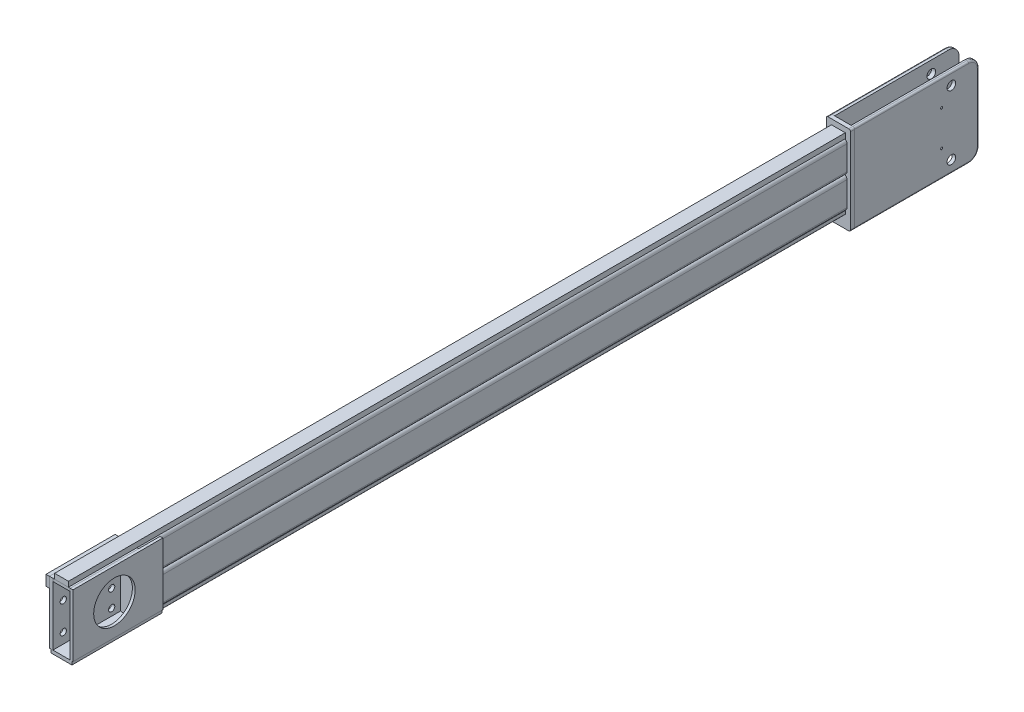
SolidWorks part; units mm, degrees
other "焊接文件夹"
material "普通碳钢"
ref_plane "前视基准面" through (0, 0, 0) normal (0, 0, 1) x (1, 0, 0)
ref_plane "上视基准面" through (0, 0, 0) normal (0, 1, 0) x (1, 0, 0)
ref_plane "右视基准面" through (0, 0, 0) normal (1, 0, 0) x (0, 0, -1)
sketch "草图1" plane through (0, 0, 0) normal (1, 0, 0) x (0, 0, -1)
  line L0 (0, 0) -> (2050, 0)
  dimension "D1" = 2050
other "矩形钢管 90×60×5(1)"
ref_plane "基准面1" through (15, 55, 0) normal (0, 0, -1) x (1, 0, 0)
sketch "草图11" plane through (15, 55, 0) normal (0, 0, -1) x (1, 0, 0)
  line L0 (-15, 50) -> (15, 50)
  line L1 (-15, -35) -> (15, -35)
  line L2 (-25, -25) -> (-25, 45)
  line L3 (-15, 55) -> (15, 55)
  line L4 (25, -25) -> (25, 45)
  line L7 (20, -25) -> (20, 45)
  line L8 (-15, -30) -> (15, -30)
  line L9 (-20, -25) -> (-20, 45)
  arc A0 (15, 55) -> (25, 45) centre (15, 45) cw
  arc A1 (15, -35) -> (25, -25) centre (15, -25) ccw
  arc A2 (-15, -35) -> (-25, -25) centre (-15, -25) cw
  arc A3 (-25, 45) -> (-15, 55) centre (-15, 45) cw
  arc A4 (-20, 45) -> (-15, 50) centre (-15, 45) cw
  arc A5 (15, 50) -> (20, 45) centre (15, 45) cw
  arc A6 (15, -30) -> (20, -25) centre (15, -25) ccw
  arc A7 (-15, -30) -> (-20, -25) centre (-15, -25) cw
  point P0 (0, 0)
  point P1 (0, 0)
  point P30 (0, 0)
  point P32 (-25, 35)
  point P33 (-25, -35)
  point P34 (25, -35)
  point P35 (25, 35)
  dimension "D3" = 10
  dimension "D1" = 50
  dimension "D2" = 90
  dimension "D4" = 5
other "矩形钢管 90×60×5(3)"
ref_plane "基准面2" through (15, -35, 0) normal (0, 0, -1) x (1, 0, 0)
sketch "草图12" plane through (15, -35, 0) normal (0, 0, -1) x (1, 0, 0)
  line L0 (-15, 50) -> (15, 50)
  line L1 (-15, -35) -> (15, -35)
  line L2 (-25, -25) -> (-25, 45)
  line L3 (-15, 55) -> (15, 55)
  line L4 (25, -25) -> (25, 45)
  line L7 (20, -25) -> (20, 45)
  line L8 (-15, -30) -> (15, -30)
  line L9 (-20, -25) -> (-20, 45)
  arc A0 (15, 55) -> (25, 45) centre (15, 45) cw
  arc A1 (15, -35) -> (25, -25) centre (15, -25) ccw
  arc A2 (-15, -35) -> (-25, -25) centre (-15, -25) cw
  arc A3 (-25, 45) -> (-15, 55) centre (-15, 45) cw
  arc A4 (-20, 45) -> (-15, 50) centre (-15, 45) cw
  arc A5 (15, 50) -> (20, 45) centre (15, 45) cw
  arc A6 (15, -30) -> (20, -25) centre (15, -25) ccw
  arc A7 (-15, -30) -> (-20, -25) centre (-15, -25) cw
  point P0 (0, 0)
  point P1 (0, 0)
  point P30 (0, 0)
  point P32 (-25, 35)
  point P33 (-25, -35)
  point P34 (25, -35)
  point P35 (25, 35)
  dimension "D3" = 10
  dimension "D1" = 50
  dimension "D2" = 90
  dimension "D4" = 5
ref_plane "基准面3" through (30, 0, 0) normal (1, 0, 0) x (0, 0, -1)
sketch "草图13" plane through (30, 0, 0) normal (1, 0, 0) x (0, 0, -1)
  line L0 (0, 0) -> (2050, 0)
sketch "草图14" plane through (0, 0, 0) normal (0, 0, 1) x (1, 0, 0)
  line L2 (45, 80) -> (45, -80)
  line L3 (0, -85) -> (40, -85)
  line L4 (-5, 80) -> (-5, -80)
  line L5 (0, 85) -> (40, 85)
  arc A0 (40, -85) -> (45, -80) centre (40, -80) ccw
  arc A1 (-5, -80) -> (0, -85) centre (0, -80) ccw
  arc A4 (0, 85) -> (-5, 80) centre (0, 80) ccw
  arc A5 (45, 80) -> (40, 85) centre (40, 80) ccw
extrude "凸台-拉伸1" add sketch "草图14" along normal blind 8 separate body
sketch "草图15" plane through (0, 0, -2050) normal (0, 0, -1) x (-1, 0, 0)
  line L0 (-50, 115) -> (-50, -131)
  line L1 (-45, 120) -> (15, 120)
  line L3 (-45, -136) -> (15, -136)
  line L5 (-40, 80) -> (-40, 10) construction
  line L6 (20, -131) -> (20, 115)
  line L7 (10, 10) -> (10, 80) construction
  line L8 (0, 90) -> (-30, 90) construction
  line L9 (-30, -90) -> (0, -90) construction
  arc A0 (15, -136) -> (20, -131) centre (15, -131) ccw
  arc A1 (-50, -131) -> (-45, -136) centre (-45, -131) ccw
  arc A2 (20, 115) -> (15, 120) centre (15, 115) ccw
  arc A3 (-50, 115) -> (-45, 120) centre (-45, 115) cw
  dimension "D5" = 5
  dimension "D1" = 30
  dimension "D2" = 10
  dimension "D3" = 10
  dimension "D4" = 46
extrude "凸台-拉伸2" add sketch "草图15" along normal blind 12 separate body
sketch "草图16" plane through (0, 0, -2062) normal (0, 0, -1) x (-1, 0, 0)
  line L0 (-45, -136) -> (15, -136) construction
  line L1 (-40, -136) -> (-50, -136)
  line L2 (-40, -136) -> (-40, 120)
  line L3 (-40, 120) -> (-50, 120)
  line L4 (-50, -136) -> (-50, 120)
  line L6 (15, 120) -> (-45, 120) construction
  line L11 (8, 120) -> (20, 120)
  line L12 (8, 120) -> (8, -136)
  line L13 (8, -136) -> (20, -136)
  line L14 (20, 120) -> (20, -136)
  line L15 (20, -131) -> (20, 115) construction
  line L16 (-50, 115) -> (-50, -131) construction
  dimension "D1" = 12
  dimension "D2" = 10
extrude "凸台-拉伸3" add sketch "草图16" along normal blind 360 separate body
fillet "圆角4" radius 30 2 edges at (45, -136, -2422) (45, 120, -2422)
fillet "圆角5" radius 30 2 edges at (-14, -136, -2422) (-14, 120, -2422)
fillet "圆角1" radius 5 5 edges at (50, -136, -2227) (50, 120, -2227) (50, -127.2132, -2413.2132) (50, -8, -2422) (50, 111.2132, -2413.2132)
fillet "圆角2" radius 5 5 edges at (-20, -136, -2227) (-20, 120, -2227) (-20, -127.2132, -2413.2132) (-20, -8, -2422) (-20, 111.2132, -2413.2132)
sketch "草图17" plane through (0, -90, 0) normal (0, -1, 0) x (1, 0, 0)
  line L0 (-10, -2050) -> (-10, 0) construction
  line L1 (35, -60) -> (-5, -60)
  line L2 (35, -60) -> (35, -2050)
  line L3 (35, -2050) -> (-5, -2050)
  line L4 (-5, -60) -> (-5, -2050)
  line L5 (30, -2050) -> (0, -2050) construction
  line L6 (30, 0) -> (0, 0) construction
  dimension "D1" = 40
  dimension "D2" = 5
  dimension "D3" = 60
extrude "凸台-拉伸4" add sketch "草图17" along normal blind 10 separate body
fillet "圆角6" radius 1 2 edges at (35, -100, -1055) (-5, -100, -1055)
sketch "草图18" plane through (-20, 0, 0) normal (-1, 0, 0) x (0, 0, 1)
  line L0 (-2342, 85) -> (-2342, -101) construction
  line L1 (-2392, 120) -> (-2062, 120) construction
  line L2 (-2062, -136) -> (-2392, -136) construction
  line L3 (-2062, -131) -> (-2062, 115) construction
  circle A0 centre (-2342, 85) radius 12.5
  circle A1 centre (-2342, -101) radius 12.5
  dimension "D1" = 25
  dimension "D2" = 25
  dimension "D3" = 35
  dimension "D4" = 35
  dimension "D5" = 280
extrude "切除-拉伸1" cut sketch "草图18" against normal up to surface (70 mm away)
sketch "草图19" plane through (50, 0, 0) normal (1, 0, 0) x (0, 0, -1)
  point P0 (2314, 42.75)
  point P1 (2314, -58.75)
hole_wizard "M6 螺纹孔1" positions "3D草图1" profile "草图20" tap size "M6" standard "GB" end condition up to next
sketch3d "3D草图1"
  point P0 (50, 42.75, -2314)
  point P3 (50, -58.75, -2314)
sketch "草图20" plane through (50, 42.75, -2314) normal (0, 1, 0) x (0, 0, -1)
  line L0 (0, 0) -> (0, 10.001)
  line L1 (0, 10.001) -> (2.5, 10.001)
  line L2 (2.5, 10.001) -> (2.5, 0.525)
  line L3 (2.5, 0.525) -> (3.025, 0)
  line L5 (3.025, 0) -> (0, 0)
  line L6 (-2.5, 0.525) -> (-3.025, 0) construction
  line L11 (0, -6.35) -> (0, 107.95) construction
  dimension "螺纹线主直径" = 5
  dimension "通孔螺纹孔钻头深度" = 10.001
  dimension "近端锥形沉头孔直径" = 6.05
  dimension "近端锥形沉头孔角度" = 90
sketch "草图21" plane through (0, 0, 8) normal (0, 0, 1) x (1, 0, 0)
  line L1 (-15, -100) -> (45, -100)
  line L2 (-15, -100) -> (-15, -90)
  line L3 (-15, -90) -> (45, -90)
  line L4 (45, -100) -> (45, -90)
  line L6 (35, -90) -> (-5, -90) construction
  line L7 (-10, -80) -> (-10, -10) construction
  line L8 (40, -10) -> (40, -80) construction
  dimension "D1" = 10
  dimension "D2" = 5
  dimension "D3" = 5
extrude "凸台-拉伸5" add sketch "草图21" along normal blind 190 separate body
ref_plane "基准面4" through (0, 0, -2) normal (0, 0, 1) x (1, 0, 0)
sketch "草图22" plane through (-10, 0, 0) normal (-1, 0, 0) x (0, 0, 1)
  line L0 (-2050, 90) -> (0, 90) construction
  line L1 (198, -90) -> (-62, -90)
  line L2 (198, -90) -> (198, 90)
  line L3 (198, 90) -> (-62, 90)
  line L4 (-62, -90) -> (-62, 90)
  dimension "D1" = 260
extrude "凸台-拉伸6" add sketch "草图22" along normal blind 10 separate body
sketch "草图23" plane through (40, 0, 0) normal (1, 0, 0) x (0, 0, -1)
  line L4 (-198, 90) -> (-198, -90)
  line L5 (-198, -90) -> (62, -90)
  line L6 (62, -90) -> (62, 90)
  line L7 (62, 90) -> (-198, 90)
  line L8 (-198, 90) -> (-198, -90)
  line L9 (-198, -90) -> (62, -90)
  line L10 (62, -90) -> (62, 90)
  line L11 (62, 90) -> (-198, 90)
  dimension "D1" = 0
extrude "凸台-拉伸7" add sketch "草图23" along normal blind 8 separate body
sketch "草图24" plane through (0, 90, 0) normal (0, 1, 0) x (1, 0, 0)
  line L1 (-10, 0) -> (40, 0)
  line L2 (-10, 0) -> (-10, -198)
  line L3 (-10, -198) -> (40, -198)
  line L4 (40, 0) -> (40, -198)
  line L6 (-10, -198) -> (-10, 62) construction
extrude "凸台-拉伸9" add sketch "草图24" against normal blind 8 separate body
sketch "草图25" plane through (48, 0, 0) normal (1, 0, 0) x (0, 0, -1)
  line L0 (-198, 90) -> (-198, -90) construction
  line L1 (-198, 0) -> (-78, 0) construction
  circle A0 centre (-78, 0) radius 60
  dimension "D1" = 120
  dimension "D2" = 120
extrude "切除-拉伸2" cut sketch "草图25" against normal up to next (8 mm away)
sketch "草图26" plane through (-20, 0, 0) normal (-1, 0, 0) x (0, 0, 1)
  line L0 (198, -60) -> (-62, -60) construction
  line L1 (28, -90) -> (28, 86.6904) construction
  line L2 (198, -90) -> (198, 90) construction
  line L4 (98, 97.709) -> (98, -90) construction
  line L5 (198, 30) -> (-62, 30) construction
  line L6 (198, -70) -> (-62, -70) construction
  line L7 (198, 20) -> (-62, 20) construction
  line L8 (198, 90) -> (-62, 90) construction
  line L9 (168, 125.1373) -> (168, -90) construction
  line L13 (-62, -90) -> (198, -90) construction
  line L14 (198, -20) -> (-62, -20) construction
  circle A6 centre (98, -20) radius 9
  circle A9 centre (98, 30) radius 9
  circle A11 centre (98, -70) radius 9
  circle A13 centre (168, -60) radius 9
  circle A14 centre (168, 20) radius 9
  circle A15 centre (28, -70) radius 9
  circle A16 centre (28, -20) radius 9
  circle A17 centre (28, 30) radius 9
  dimension "D3" = 30
  dimension "D6" = 70
  dimension "D2" = 50
  dimension "D7" = 18
  dimension "D9" = 18
  dimension "D10" = 18
  dimension "D11" = 18
  dimension "D12" = 18
  dimension "D15" = 18
  dimension "D16" = 18
  dimension "D17" = 18
  dimension "D13" = 70
  dimension "D14" = 110
  dimension "D4" = 40
  dimension "D5" = 40
  dimension "D8" = 50
extrude "切除-拉伸3" cut sketch "草图26" against normal up to next (10 mm away)
sketch "草图27" plane through (-20, 0, 0) normal (-1, 0, 0) x (0, 0, 1)
  line L6 (-2, 60) -> (198, 60)
  line L8 (198, 90) -> (198, 60)
  line L10 (-2, 90) -> (198, 90)
  line L11 (-2, 90) -> (-2, 60)
  line L14 (-2, 90) -> (-2, 245) construction
  line L15 (198, 90) -> (198, 245) construction
  line L16 (198, 90) -> (-62, 90) construction
  line L17 (198, -90) -> (198, 90) construction
  dimension "D1" = 30
  dimension "D2" = 200
extrude "凸台-拉伸10" add sketch "草图27" along normal blind 10 separate body
sketch "草图34" plane through (0, 0, 8) normal (0, 0, -1) x (-1, 0, 0)
  line L4 (15, -100) -> (15, -90)
  line L5 (15, -90) -> (-45, -90)
  line L6 (-45, -90) -> (-45, -100)
  line L7 (-45, -100) -> (15, -100)
  line L8 (15, -100) -> (15, -90)
  line L9 (15, -90) -> (-45, -90)
  line L10 (-45, -90) -> (-45, -100)
  line L11 (-45, -100) -> (15, -100)
  dimension "D1" = 0
extrude "凸台-拉伸15" add sketch "草图34" along normal up to surface (70 mm away) up to face at (-15, 0, -62)
sketch "草图28" plane through (0, 0, -2) normal (0, 0, 1) x (1, 0, 0)
  line L8 (-4, -100) -> (34, -100)
  line L9 (35, -99) -> (35, -90)
  line L10 (35, -90) -> (-5, -90)
  line L11 (-5, -90) -> (-5, -99)
  arc A4 (34, -100) -> (35, -99) centre (34, -99) ccw
  arc A5 (-5, -99) -> (-4, -100) centre (-4, -99) ccw
sketch "草图29" plane through (-20, 0, 0) normal (-1, 0, 0) x (0, 0, 1)
  line L0 (-2272, 30) -> (-2272, -70) construction
  line L1 (-2187, -70) -> (-2187, 30) construction
  line L2 (98, 30) -> (-3978.1522, 30) construction
  line L3 (-2422, -106) -> (-2422, 90) construction
  line L4 (-2102, 30) -> (-2102, -70) construction
  line L5 (-2272, -20) -> (-2102, -20) construction
  line L6 (-2272, -70) -> (-2102, -70) construction
  line L7 (-2272, -50) -> (-2102, -50) construction
  line L8 (-2272, 20) -> (-2102, 20) construction
  line L9 (-2167, -70) -> (-2167, 30) construction
  circle A3 centre (-2102, 30) radius 9
  circle A4 centre (-2102, -20) radius 9
  circle A5 centre (-2102, -70) radius 9
  circle A7 centre (-2187, -20) radius 9
  circle A8 centre (-2187, 30) radius 9
  circle A9 centre (-2272, 20) radius 9
  circle A10 centre (-2272, -50) radius 9
  circle A12 centre (-2187, -70) radius 9
  dimension "D2" = 18
  dimension "D3" = 18
  dimension "D8" = 18
  dimension "D9" = 18
  dimension "D10" = 18
  dimension "D11" = 20
  dimension "D12" = 18
  dimension "D13" = 18
  dimension "D4" = 50
  dimension "D5" = 50
  dimension "D6" = 150
  dimension "D7" = 170
  dimension "D14" = 30
  dimension "D16" = 85
  dimension "D15" = 40
extrude "切除-拉伸4" cut sketch "草图29" against normal up to next (12 mm away)
sketch "草图30" plane through (-20, 0, 0) normal (-1, 0, 0) x (0, 0, 1)
  line L0 (198, 90) -> (-2, 90) construction
  line L1 (-2372, 90) -> (-2082, 90)
  line L2 (-2372, 90) -> (-2372, 60)
  line L3 (-2372, 60) -> (-2082, 60)
  line L4 (-2082, 90) -> (-2082, 60)
  line L5 (-2, 60) -> (198, 60) construction
  line L7 (-2422, -106) -> (-2422, 90) construction
  dimension "D1" = 290
  dimension "D2" = 50
extrude "凸台-拉伸12" add sketch "草图30" along normal blind 10 separate body
sketch "草图31" plane through (0, -100, 0) normal (0, -1, 0) x (1, 0, 0)
  line L0 (-20, -62) -> (-15, -62) construction
  line L1 (40, -2) -> (-10, -2)
  line L2 (40, -2) -> (40, -62)
  line L3 (40, -62) -> (-10, -62)
  line L4 (-10, -2) -> (-10, -62)
  line L5 (40, 198) -> (40, -62) construction
  line L6 (-10, -62) -> (-10, 198) construction
  line L7 (35, -2) -> (-5, -2) construction
extrude "切除-拉伸5" cut sketch "草图31" against normal blind 10
sketch "草图32" plane through (0, 0, -2) normal (0, 0, -1) x (-1, 0, 0)
  line L8 (15, -100) -> (15, -90)
  line L9 (15, -90) -> (-45, -90)
  line L10 (-45, -90) -> (-45, -100)
  line L11 (-45, -100) -> (15, -100)
extrude "凸台-拉伸13" add sketch "草图32" along normal up to surface (60 mm away) separate body up to face at (15, -94.8018, -62)
sketch "草图33" plane through (0, 90, 0) normal (0, 1, 0) x (1, 0, 0)
  line L0 (-10, -198) -> (40, -198) construction
  line L1 (-5, -198) -> (35, -198)
  line L2 (-5, -198) -> (-5, 2050)
  line L3 (-5, 2050) -> (35, 2050)
  line L4 (35, -198) -> (35, 2050)
  line L10 (0, 2050) -> (30, 2050) construction
  line L12 (-10, 2050) -> (-10, 0) construction
  dimension "D1" = 5
  dimension "D2" = 40
extrude "凸台-拉伸14" add sketch "草图33" along normal blind 15 separate body contours L3 L4 L1 L2
hole_wizard "M8 螺纹孔的螺纹孔钻头1" positions "3D草图5" profile "草图37" hole size "M8" standard "GB" end condition up to next
sketch3d "3D草图5"
  line L0 (-5, -90, -62) -> (-5, -90, -2050) construction
  line L1 (-15, -106, -2422) -> (-15, 90, -2422) construction
  point P0 (-10, -65.5051, -1772.0192)
  point P2 (-10, -65.5051, -1852.0192)
  point P4 (-10, -25.5051, -1772.0192)
  point P6 (-10, -25.5051, -1852.0192)
  dimension "D1" = 80
  dimension "D2" = 80
  dimension "D3" = 40
  dimension "D4" = 40
  dimension "D5" = 25
  dimension "D6" = 25
  dimension "D7" = 650
  dimension "D8" = 650
sketch "草图37" plane through (-10, -65.5051, -1772.0192) normal (0, 1, 0) x (0, 0, 1)
  line L0 (0, 0) -> (0, 5.001)
  line L1 (0, 5.001) -> (3.4, 5.001)
  line L2 (3.4, 5.001) -> (3.4, 0)
  line L5 (3.4, 0) -> (0, 0)
  line L11 (0, -6.35) -> (0, 107.95) construction
  dimension "通孔孔直径" = 6.8
  dimension "通孔孔深度" = 5.001
sketch "草图38" plane through (-20, 0, 0) normal (-1, 0, 0) x (0, 0, 1)
  line L0 (-2422, -106) -> (-2422, 90) construction
  line L1 (-2392, -56) -> (-2352, -56) construction
  line L2 (-2392, -56) -> (-2392, 4) construction
  line L3 (-2392, 4) -> (-2352, 4) construction
  line L4 (-2352, -56) -> (-2352, 4) construction
  line L5 (-2062, -136) -> (-2392, -136) construction
  circle A2 centre (-2392, -56) radius 6
  circle A3 centre (-2352, -26) radius 6
  circle A4 centre (-2392, 4) radius 6
  dimension "D1" = 30
  dimension "D5" = 12
  dimension "D2" = 60
  dimension "D3" = 40
  dimension "D4" = 80
extrude "切除-拉伸6" cut sketch "草图38" against normal up to next (12 mm away)
